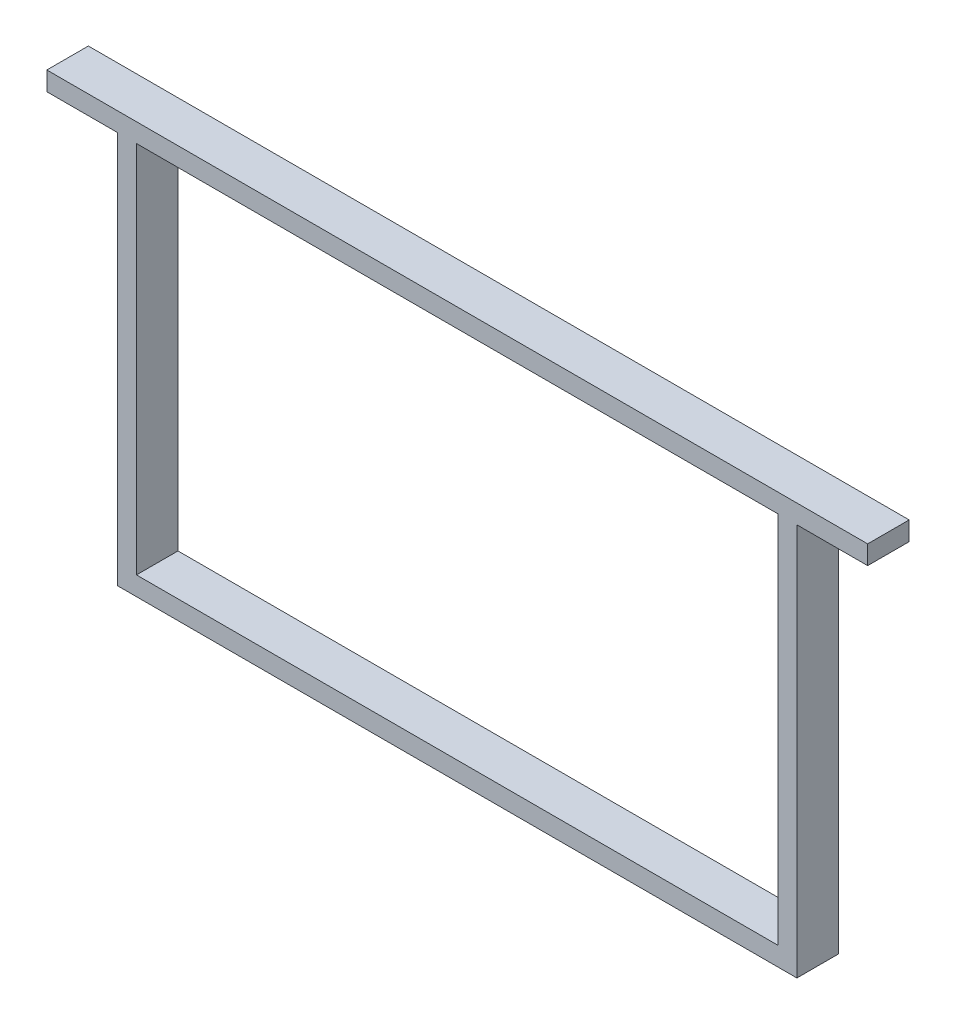
SolidWorks part; units mm, degrees
ref_plane "Front Plane" through (0, 0, 0) normal (0, 0, 1) x (1, 0, 0)
ref_plane "Top Plane" through (0, 0, 0) normal (0, 1, 0) x (1, 0, 0)
ref_plane "Right Plane" through (0, 0, 0) normal (1, 0, 0) x (0, 0, -1)
sketch "Sketch1" plane through (0, 0, 0) normal (0, 0, 1) x (1, 0, 0)
  line L0 (-217.5, 109) -> (217.5, 109)
  line L1 (217.5, 109) -> (217.5, 99)
  line L2 (217.5, 99) -> (180, 99)
  line L3 (180, 99) -> (180, -109)
  line L4 (180, -109) -> (-180, -109)
  line L5 (-180, -109) -> (-180, 99)
  line L6 (-180, 99) -> (-217.5, 99)
  line L7 (-217.5, 99) -> (-217.5, 109)
  line L8 (170, 99) -> (180, 99) construction
  line L9 (-170, -99) -> (170, -99)
  line L10 (-170, -99) -> (-170, 99)
  line L11 (-170, 99) -> (170, 99)
  line L12 (170, -99) -> (170, 99)
  line L13 (-170, -99) -> (170, 99) construction
  line L14 (-170, 99) -> (170, -99) construction
  line L15 (-170, -99) -> (-170, -109) construction
  line L16 (-170, 99) -> (-180, 99) construction
  point P0 (0, 0)
  dimension "D1" = 10
  dimension "D2" = 37.5
  dimension "D3" = 435
  dimension "D4" = 218
extrude "Boss-Extrude1" add sketch "Sketch1" along normal blind 22
